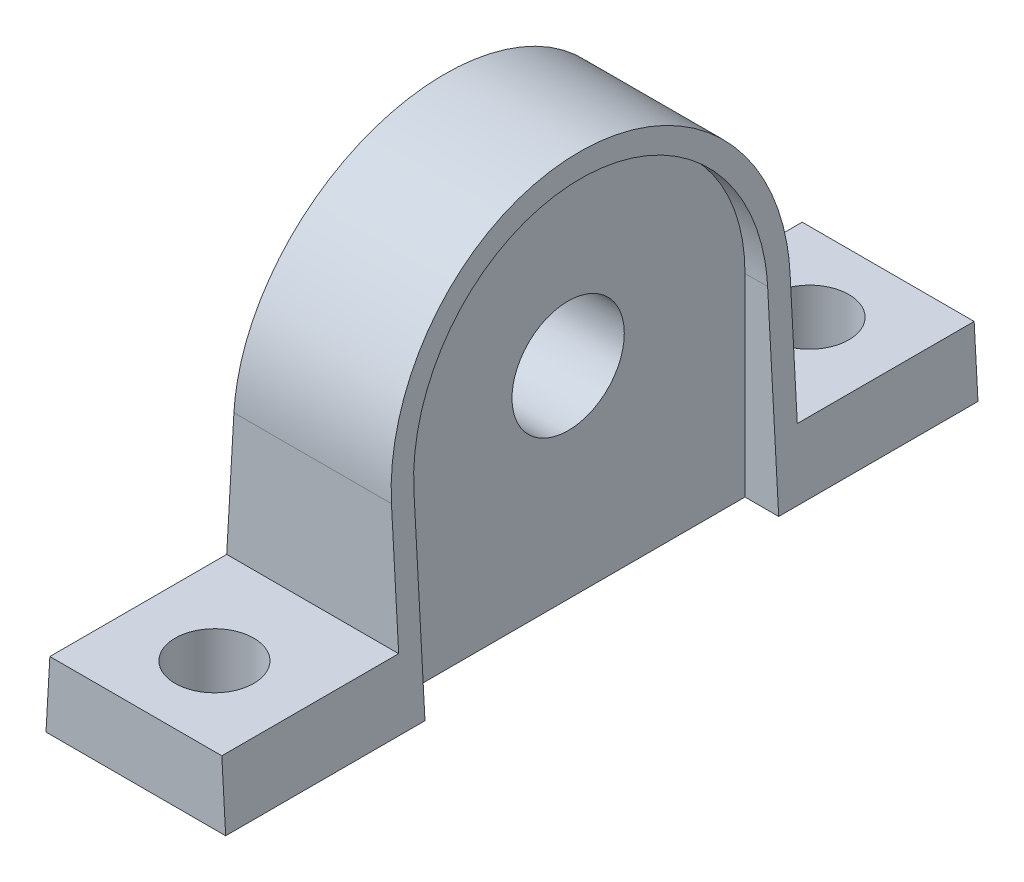
SolidWorks part; units mm, degrees
ref_plane "前视基准面" through (0, 0, 0) normal (0, 0, 1) x (1, 0, 0)
ref_plane "上视基准面" through (0, 0, 0) normal (0, 1, 0) x (1, 0, 0)
ref_plane "右视基准面" through (0, 0, 0) normal (1, 0, 0) x (0, 0, -1)
sketch "草图1" plane through (0, 0, 0) normal (0, 0, 1) x (1, 0, 0)
  line L0 (69.2331, 150.4836) -> (329.6081, 150.4836) construction
  line L1 (0, 0) -> (0, 41.7197) construction
  line L2 (8, 0) -> (-8, 0)
  line L3 (-8, 0) -> (-6, 35)
  line L4 (-6, 35) -> (6, 35)
  line L5 (8, 0) -> (6, 35)
  point P9 (0, 35)
  dimension "D1" = 8
  dimension "D2" = 6
  dimension "D3" = 35
extrude "凸台-拉伸1" add sketch "草图1" along normal blind 67
sketch "草图2" plane through (0, 0, 0) normal (1, 0, 0) x (0, 0, -1)
  line L0 (113.5531, 237.8033) -> (549.5531, 237.8033) construction
  line L1 (-33.5, 0) -> (-33.5, 43.4545) construction
  line L2 (-67, 0) -> (0, 0) construction
  line L4 (-67, 6) -> (-51.25, 6)
  line L5 (-67, 0) -> (-67, 35) construction
  line L6 (-51.25, 6) -> (-51.25, 17.25)
  line L7 (-67, 6) -> (-67, 0)
  line L8 (-67, 0) -> (0, 0)
  line L9 (0, 6) -> (0, 0)
  line L10 (0, 6) -> (-15.75, 6)
  line L11 (-15.75, 6) -> (-15.75, 17.25)
  line L12 (-67, 35) -> (0, 35) construction
  line L13 (-67, 6) -> (-67, 35)
  line L14 (-67, 35) -> (0, 35)
  line L15 (0, 35) -> (0, 6)
  arc A0 (-51.25, 17.25) -> (-15.75, 17.25) centre (-33.5, 17.25) cw
  circle A1 centre (-33.5, 18) radius 5
  dimension "D3" = 18
  dimension "D4" = 10
  dimension "D1" = 6
  dimension "D2" = 35.5
extrude "切除-拉伸1" cut sketch "草图2" against normal mid plane 30 contours L6 A0 L14 L13 L4 | L14 A0 L11 L10 L15 | A1
ref_plane "基准面1" through (8, 0, 0) normal (1, 0, 0) x (0, 0, -1)
sketch "草图3" plane through (8, 0, 0) normal (1, 0, 0) x (0, 0, -1)
  line L0 (-51.25, 17.25) -> (-51.25, 6) construction
  line L1 (-15.75, 17.25) -> (-15.75, 6) construction
  line L2 (-51.25, 17.25) -> (-51.25, 6)
  line L3 (-15.75, 17.25) -> (-15.75, 6)
  line L4 (-51.25, 6) -> (-51.25, 0)
  line L5 (-67, 0) -> (0, 0) construction
  line L6 (-51.25, 0) -> (-15.75, 0)
  line L7 (-15.75, 0) -> (-15.75, 6)
  line L8 (-49.25, 17.25) -> (-49.25, 6)
  line L9 (-49.25, 6) -> (-49.25, 0)
  line L10 (-17.75, 6) -> (-17.75, 0)
  line L12 (-17.75, 17.25) -> (-17.75, 6)
  line L13 (-49.25, 2) -> (-17.75, 2) construction
  line L14 (-49.25, 6) -> (-49.25, 2) construction
  line L15 (-17.75, 2) -> (-17.75, 6) construction
  arc A0 (-15.75, 17.25) -> (-51.25, 17.25) centre (-33.5, 17.25) ccw construction
  arc A1 (-15.75, 17.25) -> (-51.25, 17.25) centre (-33.5, 17.25) ccw
  arc A2 (-17.75, 17.25) -> (-49.25, 17.25) centre (-33.5, 17.25) ccw
  dimension "D1" = 2
extrude "切除-拉伸2" cut sketch "草图3" against normal blind 3 contours L12 A2 L8 L9 L6 L10
mirror "镜向1" about plane through (0, 0, 0) normal (1, 0, 0) of "切除-拉伸2"
ref_plane "基准面2" through (-10, 0, 0) normal (1, 0, 0) x (0, 0, -1)
sketch "草图4" plane through (-10, 0, 0) normal (1, 0, 0) x (0, 0, -1)
  line L0 (-49.25, 0) -> (-17.75, 0) construction
  line L1 (-33.5, 0) -> (-33.5, 18) construction
  circle A0 centre (-33.5, 18) radius 7
  circle A2 centre (-33.5, 18) radius 5
  dimension "D1" = 14
  dimension "D2" = 10
  dimension "D3" = 18
extrude "凸台-拉伸2" add sketch "草图4" along normal up to surface (5 mm away) up to face at (-5, 12.5625, 33.5)
sketch "草图5" plane through (0, 0, 0) normal (0, -1, 0) x (1, 0, 0)
  line L0 (-5, 33.5) -> (5, 33.5) construction
  line L1 (-5, 40.5) -> (-5, 26.5) construction
  line L2 (5, 49.25) -> (5, 17.75) construction
  line L4 (0, 33.5) -> (0, 60) construction
  circle A0 centre (0, 60) radius 3.5
  circle A1 centre (0, 7) radius 3.5
  dimension "D1" = 7
  dimension "D2" = 53
extrude "切除-拉伸4" cut sketch "草图5" against normal blind 10
